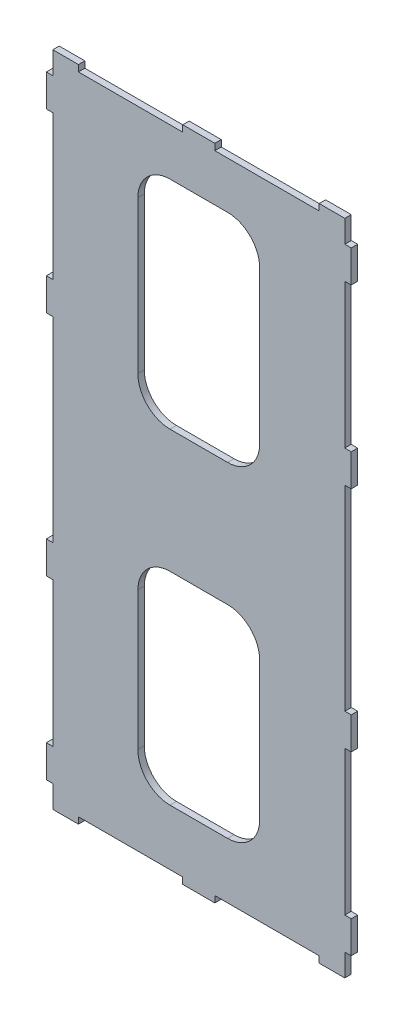
SolidWorks part; units mm, degrees
ref_plane "Front Plane" through (0, 0, 0) normal (0, 0, 1) x (1, 0, 0)
ref_plane "Top Plane" through (0, 0, 0) normal (0, 1, 0) x (1, 0, 0)
ref_plane "Right Plane" through (0, 0, 0) normal (1, 0, 0) x (0, 0, -1)
sketch "Sketch1" plane through (0, 0, 0) normal (0, 0, 1) x (1, 0, 0)
  line L0 (0, 263.7647) -> (0, -233.1278) construction
  line L2 (-75, -201) -> (-10, -201)
  line L3 (-95, -191) -> (-95, -171)
  line L5 (95, -191) -> (95, -171)
  line L10 (-95, 191) -> (-91, 191)
  line L11 (-91, 171) -> (-95, 171)
  line L12 (-95, 81) -> (-91, 81)
  line L13 (-91, 61) -> (-95, 61)
  line L14 (-95, -61) -> (-91, -61)
  line L15 (-91, -81) -> (-95, -81)
  line L16 (-95, -171) -> (-91, -171)
  line L17 (-91, -191) -> (-95, -191)
  line L18 (-91, 191) -> (-91, 205)
  line L19 (-95, 171) -> (-95, 191)
  line L20 (-91, 81) -> (-91, 171)
  line L21 (-95, 61) -> (-95, 81)
  line L22 (-91, -61) -> (-91, 61)
  line L23 (-95, -81) -> (-95, -61)
  line L24 (-91, -171) -> (-91, -81)
  line L26 (91, -191) -> (95, -191)
  line L27 (95, -171) -> (91, -171)
  line L28 (91, -171) -> (91, -81)
  line L29 (91, -81) -> (95, -81)
  line L30 (95, -61) -> (91, -61)
  line L31 (91, -61) -> (91, 61)
  line L32 (91, 61) -> (95, 61)
  line L33 (95, 81) -> (91, 81)
  line L34 (91, 81) -> (91, 171)
  line L35 (91, 171) -> (95, 171)
  line L36 (91, 191) -> (91, 205)
  line L37 (95, 191) -> (91, 191)
  line L38 (95, -81) -> (95, -61)
  line L39 (95, 61) -> (95, 81)
  line L40 (95, 171) -> (95, 191)
  line L41 (91, 205) -> (75, 205)
  line L43 (-75, 201) -> (-10, 201)
  line L46 (-75, 205) -> (-75, 201)
  line L47 (-10, 201) -> (-10, 205)
  line L48 (10, 205) -> (10, 201)
  line L49 (75, 201) -> (75, 205)
  line L51 (-75, 205) -> (-91, 205)
  line L53 (-91, 191) -> (-91, 205)
  line L55 (10, 201) -> (75, 201)
  line L56 (10, 205) -> (-10, 205)
  line L57 (0, 0) -> (175.3337, 0) construction
  line L58 (91, -205) -> (75, -205)
  line L59 (75, -201) -> (75, -205)
  line L60 (10, -205) -> (10, -201)
  line L61 (10, -205) -> (-10, -205)
  line L62 (-10, -201) -> (-10, -205)
  line L63 (-75, -205) -> (-75, -201)
  line L64 (-75, -205) -> (-91, -205)
  line L65 (10, -201) -> (75, -201)
  line L67 (-91, -191) -> (-91, -205)
  line L68 (91, -205) -> (91, -191)
  line L69 (-17.9491, 171.6978) -> (17.9491, 171.6978)
  line L70 (-37.9491, 151.6978) -> (-37.9491, 56.7417)
  line L71 (-17.9491, 36.7417) -> (17.9491, 36.7417)
  line L72 (37.9491, 151.6978) -> (37.9491, 56.7417)
  line L75 (-17.9491, -166.1801) -> (17.9491, -166.1801)
  line L76 (-37.9491, -146.1801) -> (-37.9491, -60)
  line L77 (-17.9491, -40) -> (17.9491, -40)
  line L78 (37.9491, -146.1801) -> (37.9491, -60)
  line L79 (-37.9491, -166.1801) -> (-32.6253, -159.7672) construction
  arc A0 (-17.9491, -166.1801) -> (-37.9491, -146.1801) centre (-17.9491, -146.1801) cw
  arc A1 (17.9491, -166.1801) -> (37.9491, -146.1801) centre (17.9491, -146.1801) ccw
  arc A2 (17.9491, -40) -> (37.9491, -60) centre (17.9491, -60) cw
  arc A3 (-37.9491, -60) -> (-17.9491, -40) centre (-17.9491, -60) cw
  arc A4 (-37.9491, 56.7417) -> (-17.9491, 36.7417) centre (-17.9491, 56.7417) ccw
  arc A5 (-17.9491, 171.6978) -> (-37.9491, 151.6978) centre (-17.9491, 151.6978) ccw
  arc A6 (17.9491, 36.7417) -> (37.9491, 56.7417) centre (17.9491, 56.7417) ccw
  arc A7 (17.9491, 171.6978) -> (37.9491, 151.6978) centre (17.9491, 151.6978) cw
  point P3 (0, 0)
  point P6 (-93, 191)
  point P7 (-93, -81)
  point P8 (0, -120.4673)
  point P66 (0, 122.6316)
  dimension "D1" = 20
  dimension "D2" = 190
  dimension "D3" = 410
  dimension "D4" = 14
  dimension "D5" = 14
  dimension "D6" = 20
  dimension "D7" = 20
  dimension "D8" = 90
  dimension "D9" = 20
  dimension "D10" = 90
  dimension "D11" = 20
extrude "Boss-Extrude2" add sketch "Sketch1" along normal blind 4
